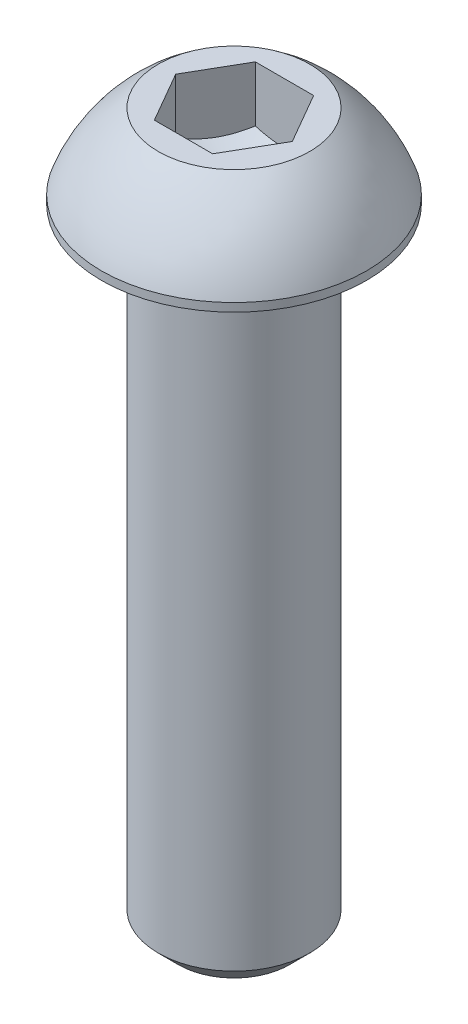
SolidWorks part; units mm, degrees
ref_plane "Ön Düzlem" through (0, 0, 0) normal (0, 0, 1) x (1, 0, 0)
ref_plane "Üst Düzlem" through (0, 0, 0) normal (0, 1, 0) x (1, 0, 0)
ref_plane "Sağ Düzlem" through (0, 0, 0) normal (1, 0, 0) x (0, 0, -1)
sketch "Çizim1" plane through (0, 0, 0) normal (0, 0, 1) x (1, 0, 0)
  line L0 (2.3094, 0) -> (3, 0)
  line L4 (3, -3.05) -> (3, -27.5)
  line L6 (2.2, -28.3) -> (0, -28.3)
  line L7 (0, -28.3) -> (0, 0) construction
  line L8 (3.25, -3.3) -> (5.25, -3.3)
  line L9 (2.3094, 0) -> (1.1547, 2) construction
  line L10 (1.1547, 2) -> (-1.1547, 2) construction
  line L11 (-1.1547, 2) -> (-2.3094, 0) construction
  line L12 (-2.3094, 0) -> (-1.1547, -2) construction
  line L13 (-1.1547, -2) -> (1.1547, -2) construction
  line L14 (1.1547, -2) -> (2.3094, 0) construction
  line L16 (3, -27.5) -> (2.2, -28.3)
  line L17 (0, -3.5333) -> (0, -28.3)
  line L18 (2.3094, 0) -> (2.3094, -2.2)
  line L19 (2.3094, -2.2) -> (0, -3.5333)
  line L20 (2.6547, 0) -> (2.6547, -1.1) construction
  line L21 (2.6547, -1.1) -> (2.6547, -2.2) construction
  line L22 (2.6547, -2.2) -> (2.6547, -3.3) construction
  line L23 (5.25, -3.3) -> (5.25, -2.97)
  circle A0 centre (0, 0) radius 2 construction
  arc A1 (3.25, -3.3) -> (3, -3.05) centre (3.25, -3.05) ccw
  arc A4 (5.25, -2.97) -> (3, 0) centre (-0.5468, -5.0242) ccw
  point P8 (3, -28.3)
  dimension "D8" = 0.25
  dimension "D12" = 6.15
  dimension "D5" = 4
  dimension "D6" = 6
  dimension "D1" = 60
  dimension "D7" = 25
  dimension "D10" = 4.6188
  dimension "D2" = 10.5
  dimension "D3" = 3.3
  dimension "D9" = 6
  dimension "D11" = 0.33
revolve "Döndür1" add sketch "Çizim1" angle 360 about L17
sketch "Çizim2" plane through (0, 0, 0) normal (0, 1, 0) x (1, 0, 0)
  line L1 (2.3094, 0) -> (1.1547, 2)
  line L2 (1.1547, 2) -> (-1.1547, 2)
  line L3 (-1.1547, 2) -> (-2.3094, 0)
  line L4 (-2.3094, 0) -> (-1.1547, -2)
  line L5 (-1.1547, -2) -> (1.1547, -2)
  line L6 (1.1547, -2) -> (2.3094, 0)
  circle A0 centre (0, 0) radius 2 construction
  circle A1 centre (0, 0) radius 3 construction
  circle A2 centre (0, 0) radius 2.3094 construction
  circle A4 centre (0, 0) radius 3
extrude "Yükseklik-Ekstrüzyon1" add sketch "Çizim2" against normal up to surface (2.2 mm away)
equation "\"M5x75\"=10"
equation "\"D11@Çizim1\"=\"D3@Çizim1\"/10"
